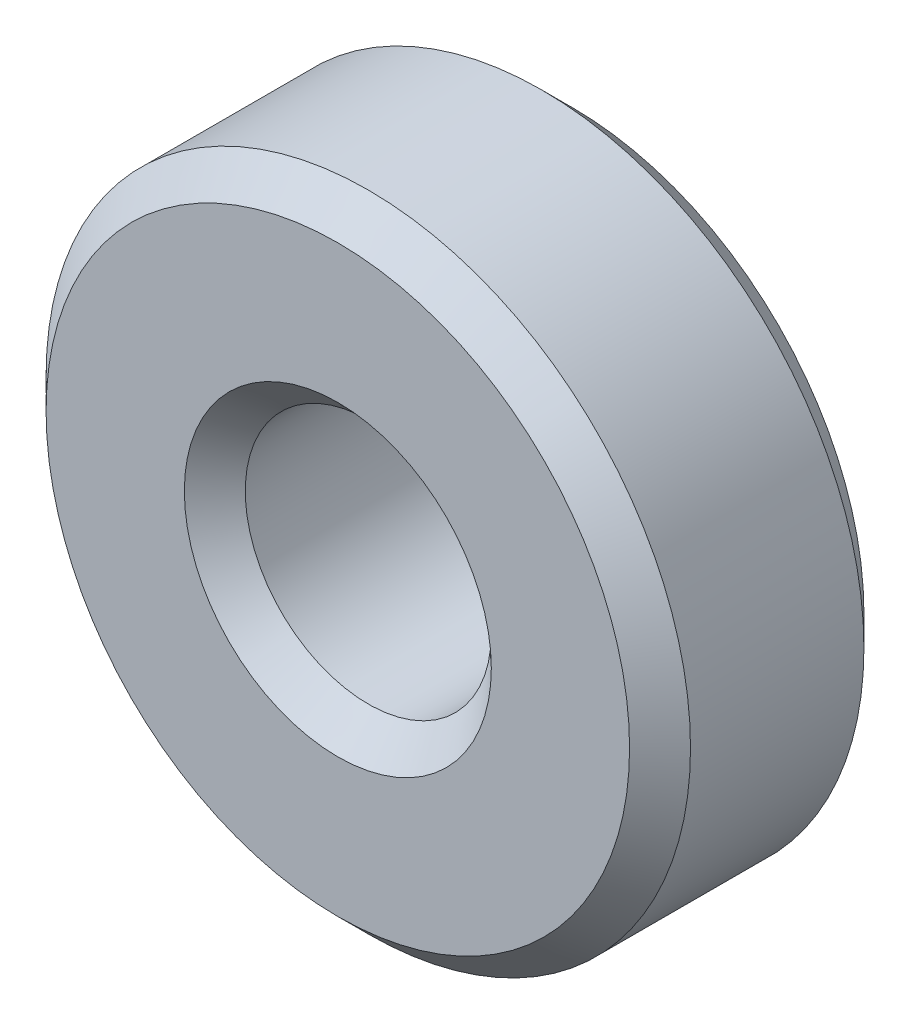
SolidWorks part; units mm, degrees
ref_plane "Front Plane" through (0, 0, 0) normal (0, 0, 1) x (1, 0, 0)
ref_plane "Top Plane" through (0, 0, 0) normal (0, 1, 0) x (1, 0, 0)
ref_plane "Right Plane" through (0, 0, 0) normal (1, 0, 0) x (0, 0, -1)
sketch "Sketch1" plane through (0, 0, 0) normal (0, 0, 1) x (1, 0, 0)
  circle A0 centre (0, 0) radius 2.625
  circle A1 centre (0, 0) radius 6.875
  dimension "D1" = 5.25
  dimension "D2" = 13.75
extrude "Boss-Extrude1" add sketch "Sketch1" along normal blind 5
chamfer "Chamfer1" distance 0.65 angle 45 4 edges at (2.625, 0, 0) (6.875, 0, 0) (2.625, 0, 5) (6.875, 0, 5)
